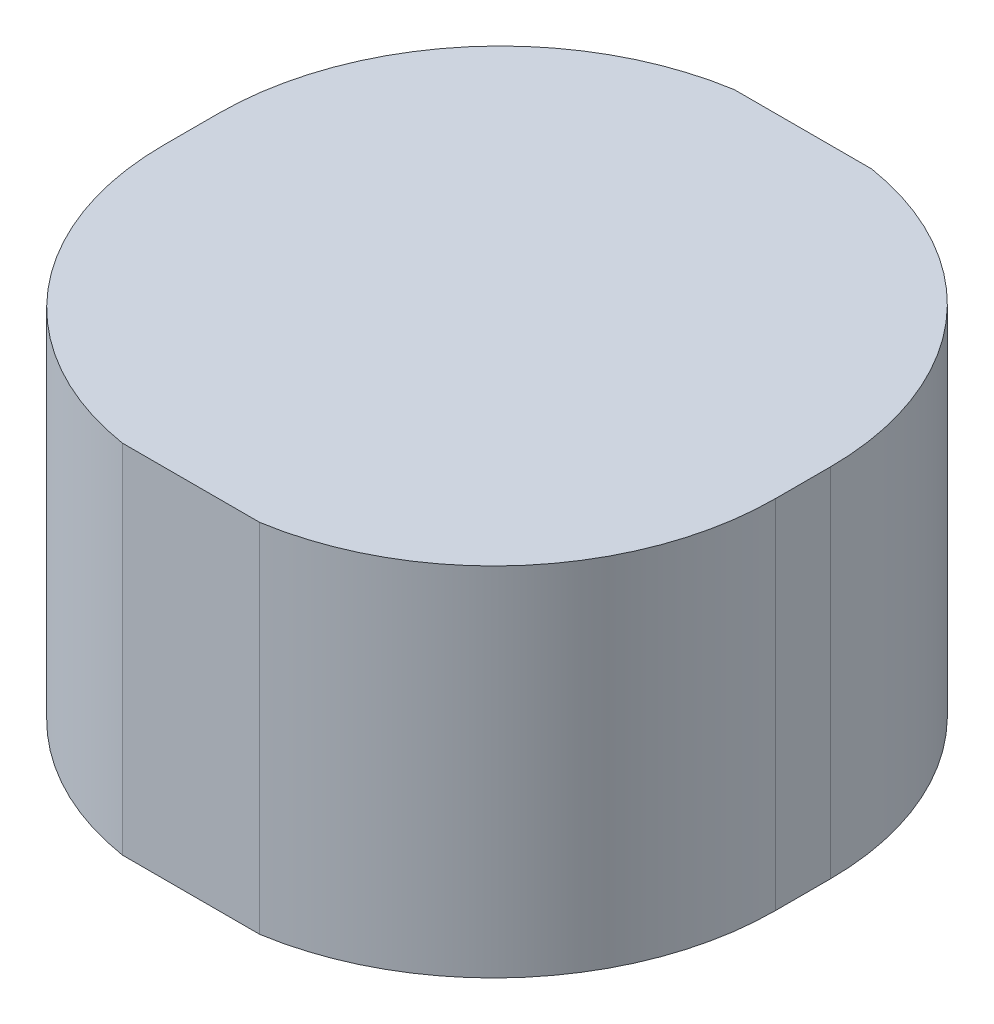
SolidWorks part; units mm, degrees
ref_plane "Front Plane" through (0, 0, 0) normal (0, 0, 1) x (1, 0, 0)
ref_plane "Top Plane" through (0, 0, 0) normal (0, 1, 0) x (1, 0, 0)
ref_plane "Right Plane" through (0, 0, 0) normal (1, 0, 0) x (0, 0, -1)
sketch "Sketch1" plane through (0, 0, 0) normal (0, 1, 0) x (1, 0, 0)
  line L0 (-111.5, -10) -> (-111.5, 10)
  line L1 (111.5, -111.5) -> (-111.5, -111.5) construction
  line L2 (111.5, -111.5) -> (111.5, 111.5) construction
  line L3 (111.5, 111.5) -> (-111.5, 111.5) construction
  line L4 (-111.5, -111.5) -> (-111.5, 111.5) construction
  line L5 (111.5, -111.5) -> (-111.5, 111.5) construction
  line L6 (111.5, 111.5) -> (-111.5, -111.5) construction
  line L7 (25, 111.5) -> (-25, 111.5)
  line L8 (0, 191.6527) -> (0, -149.2562) construction
  line L9 (-295.1271, 0) -> (200.0026, 0) construction
  line L10 (111.5, -10) -> (111.5, 10)
  line L11 (111.5, -111.5) -> (-111.5, -111.5) construction
  line L12 (25, -111.5) -> (-25, -111.5)
  arc A0 (-111.5, 10) -> (-25, 111.5) centre (-8.6994, 10) cw
  arc A1 (111.5, 10) -> (25, 111.5) centre (8.6994, 10) ccw
  arc A2 (111.5, -10) -> (25, -111.5) centre (8.6994, -10) cw
  arc A3 (-111.5, -10) -> (-25, -111.5) centre (-8.6994, -10) ccw
  point P0 (0, 0)
  point P6 (0, -111.5)
  point P8 (-111.5, 0)
  point P18 (0, 111.5)
  point P25 (111.5, 0)
  dimension "D1" = 223
  dimension "D2" = 25
  dimension "D3" = 10
extrude "Boss-Extrude1" add sketch "Sketch1" along normal blind 130
equation "\"HEADH\" = 20"
equation "\"HEADW\"= 50"
equation "\"D2@Sketch1\"=\"HEADW\"/2"
equation "\"D3@Sketch1\"=\"HEADH\"/2"
